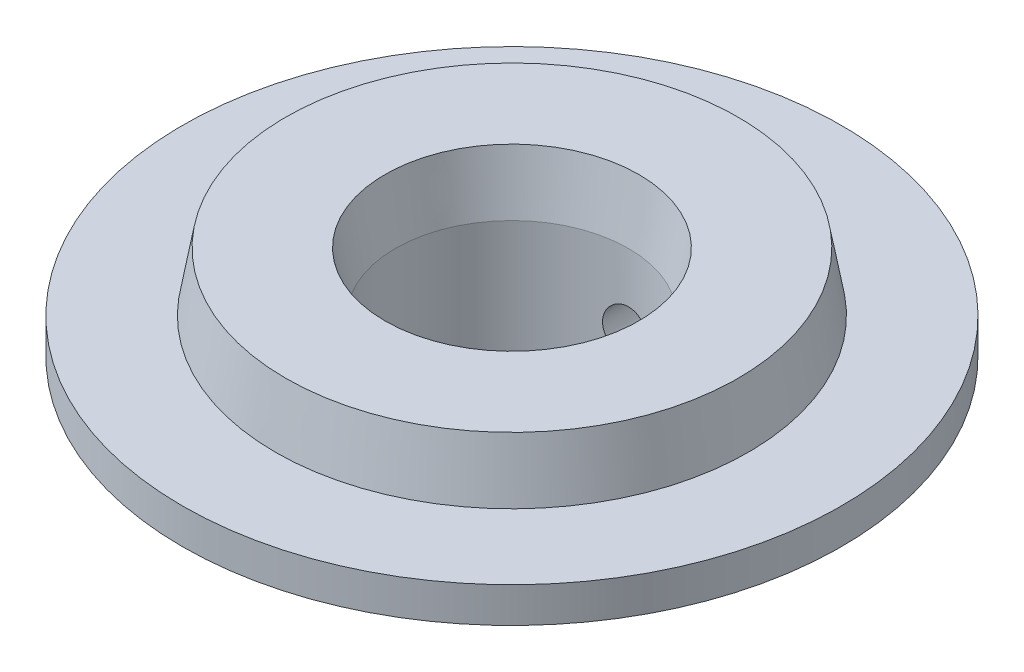
SolidWorks part; units mm, degrees
ref_plane "Спереди" through (0, 0, 0) normal (0, 0, 1) x (1, 0, 0)
ref_plane "Сверху" through (0, 0, 0) normal (0, 1, 0) x (1, 0, 0)
ref_plane "Справа" through (0, 0, 0) normal (1, 0, 0) x (0, 0, -1)
sketch "Sketch1" plane through (0, 0, 0) normal (0, 1, 0) x (1, 0, 0)
  circle A0 centre (0, 0) radius 9.9
  circle A1 centre (0, 0) radius 14
extrude "Boss-Extrude1" add sketch "Sketch1" along normal blind 7
sketch "Sketch2" plane through (0, 7, 0) normal (0, 1, 0) x (1, 0, 0)
  circle A0 centre (0, 0) radius 28
  circle A1 centre (0, 0) radius 9.9
extrude "Boss-Extrude2" add sketch "Sketch2" along normal blind 3
sketch "Sketch3" plane through (0, 10, 0) normal (0, 1, 0) x (1, 0, 0)
  circle A0 centre (0, 0) radius 9.9
  circle A1 centre (0, 0) radius 20.1
extrude "Boss-Extrude3" add sketch "Sketch3" along normal blind 5 draft 10 separate body
ref_plane "Plane1" through (0, 0, 10) normal (0, 0, 1) x (1, 0, 0)
sketch "Sketch4" plane through (0, 0, 10) normal (0, 0, 1) x (1, 0, 0)
  circle A0 centre (0, 3.7042) radius 2
extrude "Cut-Extrude1" cut sketch "Sketch4" along normal through all both and the other way through all
